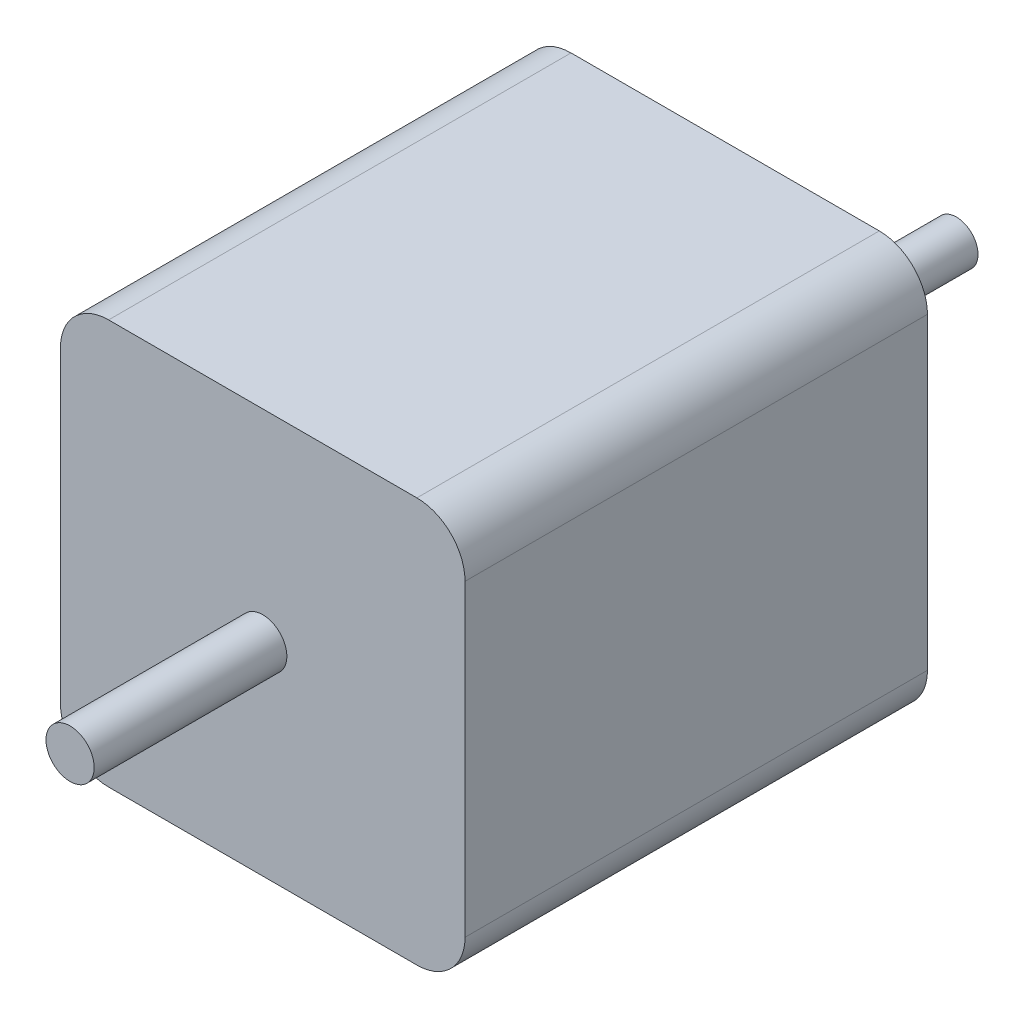
SolidWorks part; units mm, degrees
ref_plane "前视基准面" through (0, 0, 0) normal (0, 0, 1) x (1, 0, 0)
ref_plane "上视基准面" through (0, 0, 0) normal (0, 1, 0) x (1, 0, 0)
ref_plane "右视基准面" through (0, 0, 0) normal (1, 0, 0) x (0, 0, -1)
sketch "草图1" plane through (0, 0, 0) normal (0, 0, 1) x (1, 0, 0)
  line L1 (-21, -21) -> (21, -21)
  line L2 (-21, -21) -> (-21, 21)
  line L3 (-21, 21) -> (21, 21)
  line L4 (21, -21) -> (21, 21)
  line L5 (-21, -21) -> (21, 21) construction
  line L6 (-21, 21) -> (21, -21) construction
  point P0 (0, 0)
  dimension "D1" = 42
  dimension "D2" = 42
extrude "凸台-拉伸1" add sketch "草图1" along normal blind 48
sketch "草图2" plane through (0, 0, 0) normal (0, 0, -1) x (-1, 0, 0)
  circle A0 centre (0, 0) radius 11
  dimension "D1" = 22
extrude "凸台-拉伸2" add sketch "草图2" along normal blind 2
sketch "草图3" plane through (0, 0, -2) normal (0, 0, -1) x (-1, 0, 0)
  circle A0 centre (0, 0) radius 2.25
  dimension "D1" = 4.5
extrude "凸台-拉伸3" add sketch "草图3" along normal blind 22
sketch "草图4" plane through (0, 0, 0) normal (0, 0, -1) x (-1, 0, 0)
  line L0 (-14, 15.5) -> (14, 15.5) construction
  line L1 (-15.5, -15.5) -> (-14, -15.5) construction
  line L2 (-15.5, -15.5) -> (-15.5, -14) construction
  line L3 (-15.5, 15.5) -> (-14, 15.5) construction
  line L4 (15.5, -15.5) -> (15.5, -14) construction
  line L5 (-15.5, -15.5) -> (-14.4393, -14.4393) construction
  line L6 (-15.5, 15.5) -> (-14.4393, 14.4393) construction
  line L7 (14, 15.5) -> (15.5, 15.5) construction
  line L8 (-14.4393, 14.4393) -> (0, 0) construction
  line L9 (14.4393, -14.4393) -> (15.5, -15.5) construction
  line L10 (-15.5, -14) -> (-15.5, 14) construction
  line L11 (-15.5, 14) -> (-15.5, 15.5) construction
  line L12 (-14.4393, -14.4393) -> (0, 0) construction
  line L13 (0, 0) -> (14.4393, 14.4393) construction
  line L14 (-14, -15.5) -> (14, -15.5) construction
  line L15 (14, -15.5) -> (15.5, -15.5) construction
  line L16 (0, 0) -> (14.4393, -14.4393) construction
  line L17 (15.5, -14) -> (15.5, 14) construction
  line L18 (15.5, 14) -> (15.5, 15.5) construction
  line L19 (14.4393, 14.4393) -> (15.5, 15.5) construction
  circle A0 centre (-15.5, 15.5) radius 1.5
  circle A1 centre (15.5, 15.5) radius 1.5
  circle A2 centre (15.5, -15.5) radius 1.5
  circle A3 centre (-15.5, -15.5) radius 1.5
  point P0 (0, 0)
  point P16 (0, 0)
  dimension "D4" = 3
  dimension "D1" = 31
  dimension "D2" = 31
  dimension "D3" = 4
extrude "切除-拉伸1" cut sketch "草图4" against normal blind 4.5
fillet "圆角1" radius 5 4 edges at (-21, -21, 24) (21, -21, 24) (21, 21, 24) (-21, 21, 24)
sketch "草图5" plane through (0, 0, 48) normal (0, 0, 1) x (1, 0, 0)
  circle A0 centre (0, 0) radius 2.5
extrude "凸台-拉伸4" add sketch "草图5" along normal blind 20
